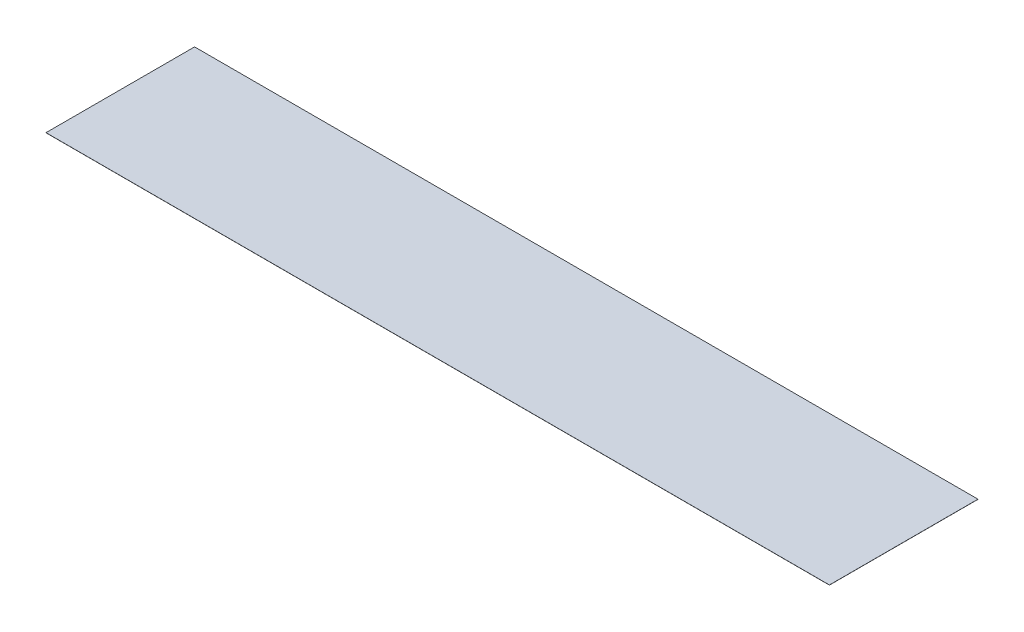
SolidWorks part; units mm, degrees
material "1060 Alloy"
ref_plane "Front Plane" through (0, 0, 0) normal (0, 0, 1) x (1, 0, 0)
ref_plane "Top Plane" through (0, 0, 0) normal (0, 1, 0) x (1, 0, 0)
ref_plane "Right Plane" through (0, 0, 0) normal (1, 0, 0) x (0, 0, -1)
sketch "Sketch1" plane through (0, 0, 0) normal (0, 1, 0) x (1, 0, 0)
  line L1 (0, 0) -> (580, 0)
  line L2 (0, 0) -> (0, 110)
  line L3 (0, 110) -> (580, 110)
  line L4 (580, 0) -> (580, 110)
  dimension "D1" = 580
  dimension "D2" = 110
extrude "Boss-Extrude1" add sketch "Sketch1" along normal blind 0.1
